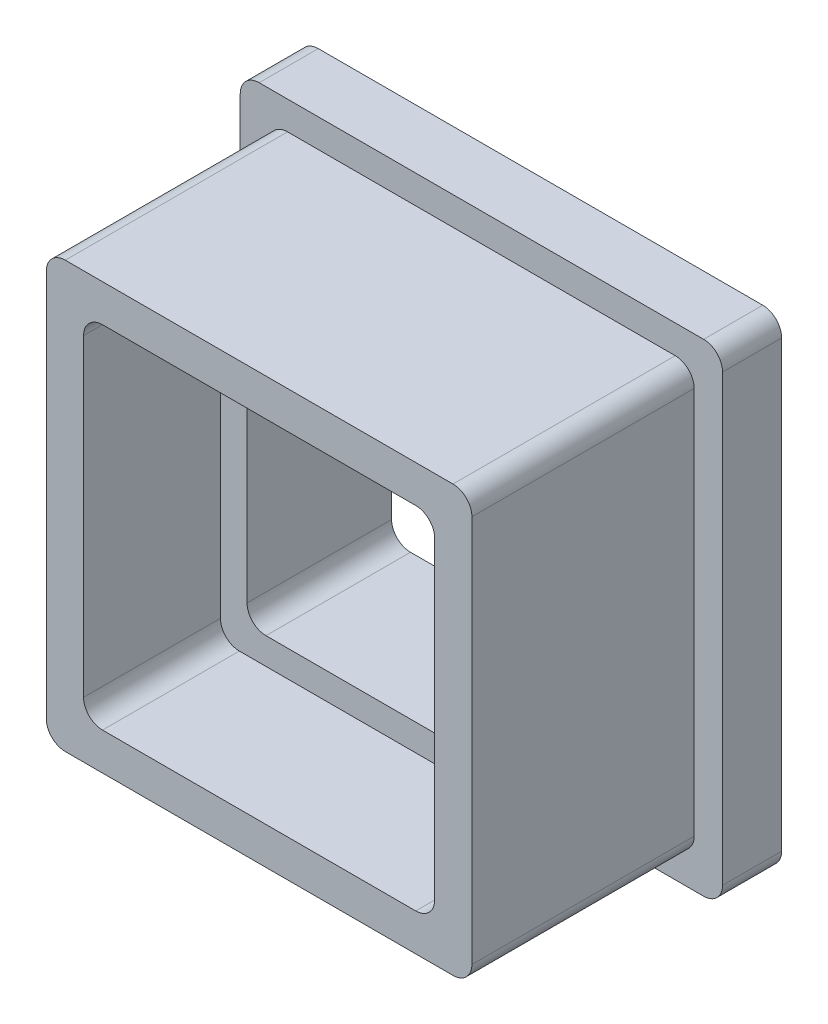
SolidWorks part; units mm, degrees
material "Nylon 101"
ref_plane "Front Plane" through (0, 0, 0) normal (0, 0, 1) x (1, 0, 0)
ref_plane "Top Plane" through (0, 0, 0) normal (0, 1, 0) x (1, 0, 0)
ref_plane "Right Plane" through (0, 0, 0) normal (1, 0, 0) x (0, 0, -1)
sketch "Sketch1" plane through (0, 0, 0) normal (0, 0, 1) x (1, 0, 0)
  line L1 (-5.715, 5.715) -> (5.715, 5.715)
  line L2 (-5.715, 5.715) -> (-5.715, -5.715)
  line L3 (-5.715, -5.715) -> (5.715, -5.715)
  line L4 (5.715, 5.715) -> (5.715, -5.715)
  line L5 (-5.715, 5.715) -> (5.715, -5.715) construction
  line L6 (-5.715, -5.715) -> (5.715, 5.715) construction
  point P0 (0, 0)
  dimension "D1" = 11.43
  dimension "D2" = 11.43
extrude "Boss-Extrude1" add sketch "Sketch1" along normal blind 4.7625 and the other way blind 1.5875
sketch "Sketch2" plane through (0, 0, -1.5875) normal (0, 0, -1) x (-1, 0, 0)
  line L0 (-6.477, 6.477) -> (-6.477, -6.477)
  line L1 (-6.477, -6.477) -> (6.477, -6.477)
  line L2 (6.477, -6.477) -> (6.477, 6.477)
  line L3 (6.477, 6.477) -> (-6.477, 6.477)
  line L4 (-5.715, 5.715) -> (-5.715, -5.715)
  line L5 (-5.715, -5.715) -> (5.715, -5.715)
  line L6 (5.715, -5.715) -> (5.715, 5.715)
  line L7 (5.715, 5.715) -> (-5.715, 5.715)
  line L8 (-5.715, 5.715) -> (-5.715, -5.715) construction
  line L9 (-5.715, -5.715) -> (5.715, -5.715) construction
  line L10 (5.715, -5.715) -> (5.715, 5.715) construction
  line L11 (5.715, 5.715) -> (-5.715, 5.715) construction
  dimension "D1" = 0
  dimension "D2" = 0.762
extrude "Boss-Extrude2" add sketch "Sketch2" along normal blind 1.5875
sketch "Sketch3" plane through (0, 0, 4.7625) normal (0, 0, 1) x (1, 0, 0)
  line L0 (5.207, -5.207) -> (5.207, 5.207)
  line L1 (5.207, 5.207) -> (-5.207, 5.207)
  line L2 (-5.207, 5.207) -> (-5.207, -5.207)
  line L3 (-5.207, -5.207) -> (5.207, -5.207)
  line L4 (5.715, -5.715) -> (5.715, 5.715)
  line L5 (5.715, 5.715) -> (-5.715, 5.715)
  line L6 (-5.715, 5.715) -> (-5.715, -5.715)
  line L7 (-5.715, -5.715) -> (5.715, -5.715)
  line L8 (5.715, -5.715) -> (5.715, 5.715) construction
  line L9 (5.715, 5.715) -> (-5.715, 5.715) construction
  line L10 (-5.715, 5.715) -> (-5.715, -5.715) construction
  line L11 (-5.715, -5.715) -> (5.715, -5.715) construction
  dimension "D1" = 0
  dimension "D2" = 0.508
extrude "Cut-Extrude1" [suppressed] cut sketch "Sketch3" against normal blind 1.8415
sketch "Sketch6" plane through (0, 0, -3.175) normal (0, 0, -1) x (-1, 0, 0)
  line L0 (-6.477, 6.477) -> (6.477, -6.477) construction
  line L2 (1.27, -1.27) -> (-1.27, -1.27)
  line L3 (1.27, -1.27) -> (1.27, 1.27)
  line L4 (1.27, 1.27) -> (-1.27, 1.27)
  line L5 (-1.27, -1.27) -> (-1.27, 1.27)
  line L6 (1.27, -1.27) -> (-1.27, 1.27) construction
  line L7 (1.27, 1.27) -> (-1.27, -1.27) construction
  point P4 (0, 0)
  dimension "D1" = 2.54
  dimension "D2" = 2.54
sketch "Sketch7" [suppressed] plane through (0, 0, 2.921) normal (0, 0, 1) x (1, 0, 0)
  line L0 (7.3025, 7.3025) -> (-7.3025, -7.3025) construction
  line L1 (4.445, -4.445) -> (-4.445, -4.445)
  line L2 (4.445, -4.445) -> (4.445, 4.445)
  line L3 (4.445, 4.445) -> (-4.445, 4.445)
  line L4 (-4.445, -4.445) -> (-4.445, 4.445)
  line L5 (4.445, -4.445) -> (-4.445, 4.445) construction
  line L6 (4.445, 4.445) -> (-4.445, -4.445) construction
  line L7 (-5.207, 5.207) -> (-5.207, -5.207) construction
  line L8 (5.207, 5.207) -> (-5.207, 5.207) construction
  point P0 (0, 0)
  dimension "D1" = 0.762
  dimension "D2" = 0.762
loft "Cut-Loft1" [suppressed] cut profiles "Sketch7", "Sketch6"
fillet "Fillet1" [suppressed] radius 0.508
sketch "Sketch8" [suppressed] plane through (0, 0, 0) normal (1, 0, 0) x (0, 0, -1)
  line L0 (-4.7625, -5.207) -> (-4.7625, -5.715) construction
  line L1 (-4.7625, -5.207) -> (1.5875, -5.207) construction
  line L2 (1.5875, -5.715) -> (-4.7625, -5.715) construction
  line L3 (-4.5085, -5.207) -> (-4.7625, -5.207)
  line L4 (-4.7625, -5.207) -> (-4.7625, -5.715) construction
  line L5 (-4.7625, -5.715) -> (-4.5085, -5.715)
  line L6 (-4.7625, -5.207) -> (-4.7879, -5.207)
  line L7 (-4.7879, -5.207) -> (-4.7879, -5.715)
  line L8 (-4.7879, -5.715) -> (-4.7625, -5.715)
  arc A0 (-4.5085, -5.207) -> (-4.5085, -5.715) centre (-4.5085, -5.461) ccw
  dimension "D1" = 0.0254
sketch "Sketch9" plane through (0, 0, 4.7625) normal (0, 0, 1) x (1, 0, 0)
  line L4 (5.715, 5.715) -> (-5.715, 5.715)
  line L5 (-5.715, 5.715) -> (-5.715, -5.715)
  line L6 (-5.715, -5.715) -> (5.715, -5.715)
  line L7 (5.715, -5.715) -> (5.715, 5.715)
  line L8 (5.715, 5.715) -> (-5.715, 5.715)
  line L9 (-5.715, 5.715) -> (-5.715, -5.715)
  line L10 (-5.715, -5.715) -> (5.715, -5.715)
  line L11 (5.715, -5.715) -> (5.715, 5.715)
  dimension "D1" = 0
sweep "Cut-Sweep2" [suppressed] cut profiles "Sketch8" path "Sketch9"
sketch "Sketch10" [suppressed] plane through (0, 0, 2.921) normal (0, 0, 1) x (1, 0, 0)
  line L0 (-4.3153, 3.8458) -> (-4.3153, -3.8458) construction
  line L1 (-4.3153, -3.8458) -> (-1.27, -0.8005) construction
  line L2 (-1.27, -0.8005) -> (-1.27, 0.8005) construction
  line L3 (-1.27, 0.8005) -> (-4.3153, 3.8458) construction
  line L4 (-0.8005, 1.27) -> (0.8005, 1.27) construction
  line L5 (0.8005, 1.27) -> (3.8458, 4.3153) construction
  line L6 (3.8458, 4.3153) -> (-3.8458, 4.3153) construction
  line L7 (-3.8458, 4.3153) -> (-0.8005, 1.27) construction
  line L8 (1.27, 0.8005) -> (1.27, -0.8005) construction
  line L9 (1.27, -0.8005) -> (4.3153, -3.8458) construction
  line L10 (4.3153, -3.8458) -> (4.3153, 3.8458) construction
  line L11 (4.3153, 3.8458) -> (1.27, 0.8005) construction
  line L12 (0.8005, -1.27) -> (-0.8005, -1.27) construction
  line L13 (-0.8005, -1.27) -> (-3.8458, -4.3153) construction
  line L14 (-3.8458, -4.3153) -> (3.8458, -4.3153) construction
  line L15 (3.8458, -4.3153) -> (0.8005, -1.27) construction
  line L16 (-4.3153, 3.8458) -> (-4.3153, -3.8458) construction
  line L17 (-4.3153, -3.8458) -> (-1.27, -0.8005) construction
  line L18 (-1.27, -0.8005) -> (-1.27, 0.8005) construction
  line L19 (-1.27, 0.8005) -> (-4.3153, 3.8458) construction
  line L20 (-0.8005, 1.27) -> (0.8005, 1.27) construction
  line L21 (0.8005, 1.27) -> (3.8458, 4.3153) construction
  line L22 (3.8458, 4.3153) -> (-3.8458, 4.3153) construction
  line L23 (-3.8458, 4.3153) -> (-0.8005, 1.27) construction
  line L24 (1.27, 0.8005) -> (1.27, -0.8005) construction
  line L25 (1.27, -0.8005) -> (4.3153, -3.8458) construction
  line L26 (4.3153, -3.8458) -> (4.3153, 3.8458) construction
  line L27 (4.3153, 3.8458) -> (1.27, 0.8005) construction
  line L28 (0.8005, -1.27) -> (-0.8005, -1.27) construction
  line L29 (-0.8005, -1.27) -> (-3.8458, -4.3153) construction
  line L30 (-3.8458, -4.3153) -> (3.8458, -4.3153) construction
  line L31 (3.8458, -4.3153) -> (0.8005, -1.27) construction
  line L32 (-3.5533, 2.0061) -> (-3.5533, -2.0061)
  line L33 (-3.5533, -2.0061) -> (-2.032, -0.4849)
  line L34 (-2.032, -0.4849) -> (-2.032, 0.4849)
  line L35 (-2.032, 0.4849) -> (-3.5533, 2.0061)
  line L36 (-0.4849, 2.032) -> (0.4849, 2.032)
  line L37 (0.4849, 2.032) -> (2.0061, 3.5533)
  line L38 (2.0061, 3.5533) -> (-2.0061, 3.5533)
  line L39 (-2.0061, 3.5533) -> (-0.4849, 2.032)
  line L40 (2.032, 0.4849) -> (2.032, -0.4849)
  line L41 (2.032, -0.4849) -> (3.5533, -2.0061)
  line L42 (3.5533, -2.0061) -> (3.5533, 2.0061)
  line L43 (3.5533, 2.0061) -> (2.032, 0.4849)
  line L44 (0.4849, -2.032) -> (-0.4849, -2.032)
  line L45 (-0.4849, -2.032) -> (-2.0061, -3.5533)
  line L46 (-2.0061, -3.5533) -> (2.0061, -3.5533)
  line L47 (2.0061, -3.5533) -> (0.4849, -2.032)
  dimension "D1" = 0.762
extrude "Cut-Extrude2" [suppressed] cut sketch "Sketch10" against normal offset from surface (6.4135 mm away) 1.27
fillet "Fillet4" [suppressed] radius 0.254
fillet "Fillet5" [suppressed] radius 0.254
sketch "Sketch11" [suppressed] plane through (0, 0, 2.921) normal (0, 0, 1) x (1, 0, 0)
  line L1 (2.54, -2.54) -> (-2.54, -2.54)
  line L2 (2.54, -2.54) -> (2.54, 2.54)
  line L3 (2.54, 2.54) -> (-2.54, 2.54)
  line L4 (-2.54, -2.54) -> (-2.54, 2.54)
  line L5 (2.54, -2.54) -> (-2.54, 2.54) construction
  line L6 (2.54, 2.54) -> (-2.54, -2.54) construction
  point P0 (0, 0)
  dimension "D1" = 5.08
  dimension "D2" = 5.08
extrude "Cut-Extrude3" [suppressed] cut sketch "Sketch11" against normal through all draft 5
sketch "Sketch12" [suppressed] plane through (0, 0, 2.921) normal (0, 0, 1) x (1, 0, 0)
  line L0 (-5.207, 0) -> (5.207, 0)
  line L1 (-5.207, 5.207) -> (-5.207, -5.207) construction
  line L2 (5.207, -5.207) -> (5.207, 5.207) construction
  line L3 (0, 5.207) -> (0, -5.207)
  line L4 (5.207, 5.207) -> (-5.207, 5.207) construction
  line L5 (-5.207, -5.207) -> (5.207, -5.207) construction
extrude "Cut-Extrude-Thin1" [suppressed] cut sketch "Sketch12" against normal offset from surface (6.4135 mm away) 1.27 thin
fillet "Fillet6" [suppressed] radius 0.508
sketch "Sketch13" [suppressed] plane through (0, 0, 0) normal (1, 0, 0) x (0, 0, -1)
  line L0 (1.5875, -5.715) -> (-4.7625, -5.715) construction
  line L1 (-2.921, -5.207) -> (-4.7625, -5.207) construction
  line L2 (-4.7625, -5.715) -> (-4.7625, 5.715) construction
  line L3 (-4.5085, -5.207) -> (-5.0165, -5.207)
  line L4 (-5.0165, -5.207) -> (-5.0165, -5.715)
  line L5 (-5.0165, -5.715) -> (-4.5085, -5.715)
  arc A0 (-4.5085, -5.207) -> (-4.5085, -5.715) centre (-4.5085, -5.461) ccw
  dimension "D1" = 0.508
sketch "Sketch14" plane through (0, 0, 4.7625) normal (0, 0, 1) x (1, 0, 0)
  line L4 (5.715, -5.715) -> (5.715, 5.715)
  line L5 (5.715, 5.715) -> (-5.715, 5.715)
  line L6 (-5.715, 5.715) -> (-5.715, -5.715)
  line L7 (-5.715, -5.715) -> (5.715, -5.715)
  line L8 (5.715, -5.715) -> (5.715, 5.715)
  line L9 (5.715, 5.715) -> (-5.715, 5.715)
  line L10 (-5.715, 5.715) -> (-5.715, -5.715)
  line L11 (-5.715, -5.715) -> (5.715, -5.715)
  dimension "D1" = 0
sweep "Cut-Sweep3" [suppressed] cut profiles "Sketch13" path "Sketch14"
shell "Shell1" [suppressed] thickness 1
sketch "Sketch15" plane through (0, 0, -3.175) normal (0, 0, -1) x (-1, 0, 0)
  circle A0 centre (0, 0) radius 1.5
  dimension "D1" = 3
extrude "Boss-Extrude3" [suppressed] add sketch "Sketch15" against normal offset from surface (6.1595 mm away) 1.778 separate body
sketch "Sketch16" [suppressed] plane through (0, 0, 2.9845) normal (0, 0, 1) x (1, 0, 0)
  line L0 (0, 4.715) -> (0, -4.715)
  line L1 (4.715, 4.715) -> (-4.715, 4.715) construction
  line L2 (-4.715, -4.715) -> (4.715, -4.715) construction
  line L4 (4.715, -4.715) -> (4.715, 4.715) construction
  line L5 (4.715, 0) -> (-4.715, 0)
  line L6 (-4.715, 4.715) -> (-4.715, -4.715) construction
extrude "Extrude-Thin1" [suppressed] add sketch "Sketch16" against normal up to surface (6.1595 mm away) thin
sketch "Sketch17" [suppressed] plane through (0, 0, -3.175) normal (0, 0, -1) x (-1, 0, 0)
  line L1 (4.715, 4.715) -> (-4.715, 4.715)
  line L2 (-4.715, 4.715) -> (-4.715, -4.715)
  line L3 (-4.715, -4.715) -> (4.715, -4.715)
  line L4 (4.715, -4.715) -> (4.715, 4.715)
  line L5 (5.477, 5.477) -> (-5.477, 5.477)
  line L6 (-5.477, 5.477) -> (-5.477, -5.477)
  line L8 (-5.477, -5.477) -> (5.477, -5.477)
  line L9 (5.477, -5.477) -> (5.477, 5.477)
  line L10 (5.477, 5.477) -> (-5.477, 5.477)
  line L11 (-5.477, 5.477) -> (-5.477, -5.477)
  line L12 (-5.477, -5.477) -> (5.477, -5.477)
  line L13 (5.477, -5.477) -> (5.477, 5.477)
  dimension "D1" = 0
  dimension "D2" = 0.762
extrude "Boss-Extrude4" [suppressed] add sketch "Sketch17" against normal up to next
sketch "Sketch18" [suppressed] plane through (0, 0, 2.9845) normal (0, 0, 1) x (1, 0, 0)
  circle A0 centre (0, 0) radius 0.5
  arc A3 (0.5, -1.4142) -> (1.4142, -0.5) centre (0, 0) ccw construction
  dimension "D1" = 1
extrude "Cut-Extrude4" [suppressed] cut sketch "Sketch18" against normal through all
fillet "Fillet8" [suppressed] radius 0.508
sketch "Sketch20" plane through (0, 0, -3.175) normal (0, 0, -1) x (-1, 0, 0)
  circle A0 centre (0, 0) radius 0.635
  dimension "D1" = 1.27
split line "Split Line1" [suppressed]
dome "Dome2" [suppressed] faces to dome 1 distance 0.635 parameters "D1"=0.635
hole_wizard "#56 (0.0465) Diameter Hole1" [suppressed] positions "Sketch22" profile "Sketch21" hole size "#56" standard "ANSI Inch"
sketch "Sketch22" [suppressed] plane through (0, 0, 2.9845) normal (0, 0, 1) x (1, 0, 0)
  point P0 (0, 0)
sketch "Sketch21" plane through (0, 0, 2.9845) normal (1, 0, 0) x (0, -1, 0)
  line L0 (0, 0) -> (0, 6.1595)
  line L1 (0, 6.1595) -> (0.5905, 6.1595)
  line L2 (0.5905, 6.1595) -> (0.5905, 0)
  line L5 (0.5905, 0) -> (0, 0)
  line L11 (0, -6.35) -> (0, 107.95) construction
  dimension "Thru Hole Dia." = 1.1811
  dimension "Thru Hole Depth" = 6.1595
sketch "Sketch23" plane through (0, 0, 4.7625) normal (0, 0, 1) x (1, 0, 0)
  line L1 (2.05, -1.75) -> (-2.05, -1.75)
  line L2 (2.05, -1.75) -> (2.05, 1.75)
  line L3 (2.05, 1.75) -> (-2.05, 1.75)
  line L4 (-2.05, -1.75) -> (-2.05, 1.75)
  line L5 (2.05, -1.75) -> (-2.05, 1.75) construction
  line L6 (2.05, 1.75) -> (-2.05, -1.75) construction
  point P0 (0, 0)
  dimension "D1" = 4.1
  dimension "D2" = 3.5
extrude "Cut-Extrude5" cut sketch "Sketch23" against normal through all
sketch "Sketch24" plane through (0, 0, -3.175) normal (0, 0, -1) x (-1, 0, 0)
  line L1 (3.127, -2.377) -> (-3.127, -2.377)
  line L2 (3.127, -2.377) -> (3.127, 2.377)
  line L3 (3.127, 2.377) -> (-3.127, 2.377)
  line L4 (-3.127, -2.377) -> (-3.127, 2.377)
  line L5 (3.127, -2.377) -> (-3.127, 2.377) construction
  line L6 (3.127, 2.377) -> (-3.127, -2.377) construction
  point P0 (0, 0)
  dimension "D1" = 6.254
  dimension "D2" = 4.754
extrude "Cut-Extrude6" cut sketch "Sketch24" against normal blind 4.15
sketch "Sketch25" plane through (0, 0, 4.7625) normal (0, 0, 1) x (1, 0, 0)
  line L1 (-4.715, 4.715) -> (4.715, 4.715)
  line L2 (-4.715, 4.715) -> (-4.715, -4.715)
  line L3 (-4.715, -4.715) -> (4.715, -4.715)
  line L4 (4.715, 4.715) -> (4.715, -4.715)
  line L5 (-4.715, 4.715) -> (4.715, -4.715) construction
  line L6 (-4.715, -4.715) -> (4.715, 4.715) construction
  point P0 (0, 0)
  dimension "D1" = 9.43
  dimension "D2" = 9.43
extrude "Cut-Extrude7" cut sketch "Sketch25" against normal blind 4.056
sketch "Sketch26" plane through (0, 0, -3.175) normal (0, 0, -1) x (-1, 0, 0)
  line L1 (4, 4) -> (-4, 4)
  line L2 (4, 4) -> (4, -4)
  line L3 (4, -4) -> (-4, -4)
  line L4 (-4, 4) -> (-4, -4)
  line L5 (4, 4) -> (-4, -4) construction
  line L6 (4, -4) -> (-4, 4) construction
  point P0 (0, 0)
  dimension "D1" = 8
extrude "Cut-Extrude8" cut sketch "Sketch26" against normal through all
fillet "Fillet7" radius 0.508 16 edges at (-6.477, -6.477, -2.3812) (-5.715, -5.715, 1.5875) (5.715, -5.715, 1.5875) (6.477, -6.477, -2.3812) (5.715, 5.715, 1.5875) (6.477, 6.477, -2.3812) (-6.477, 6.477, -2.3812) (-5.715, 5.715, 1.5875) (-4.715, -4.715, 2.7345) (-4.715, 4.715, 2.7345) (4.715, 4.715, 2.7345) (4, 4, -1.2343) (-4, 4, -1.2343) (-4, -4, -1.2343) (4, -4, -1.2343) (4.715, -4.715, 2.7345)
sketch "Sketch27" plane through (0, 0, 4.7625) normal (0, 0, 1) x (1, 0, 0)
  line L4 (-5.715, 5.207) -> (-5.715, -5.207)
  line L5 (-5.207, -5.715) -> (5.207, -5.715)
  line L6 (5.715, -5.207) -> (5.715, 5.207)
  line L7 (5.207, 5.715) -> (-5.207, 5.715)
  line L8 (-5.715, 5.207) -> (-5.715, -5.207)
  line L9 (-5.207, -5.715) -> (5.207, -5.715)
  line L10 (5.715, -5.207) -> (5.715, 5.207)
  line L11 (5.207, 5.715) -> (-5.207, 5.715)
  arc A4 (-5.715, -5.207) -> (-5.207, -5.715) centre (-5.207, -5.207) ccw
  arc A5 (5.207, -5.715) -> (5.715, -5.207) centre (5.207, -5.207) ccw
  arc A6 (5.715, 5.207) -> (5.207, 5.715) centre (5.207, 5.207) ccw
  arc A7 (-5.207, 5.715) -> (-5.715, 5.207) centre (-5.207, 5.207) ccw
  arc A8 (-5.715, -5.207) -> (-5.207, -5.715) centre (-5.207, -5.207) ccw
  arc A9 (5.207, -5.715) -> (5.715, -5.207) centre (5.207, -5.207) ccw
  arc A10 (5.715, 5.207) -> (5.207, 5.715) centre (5.207, 5.207) ccw
  arc A11 (-5.207, 5.715) -> (-5.715, 5.207) centre (-5.207, 5.207) ccw
  dimension "D1" = 0
extrude "Cut-Extrude9" cut sketch "Sketch27" against normal blind 0.38
equation "\"D2@Sketch7\"=\"D1@Sketch7\""
